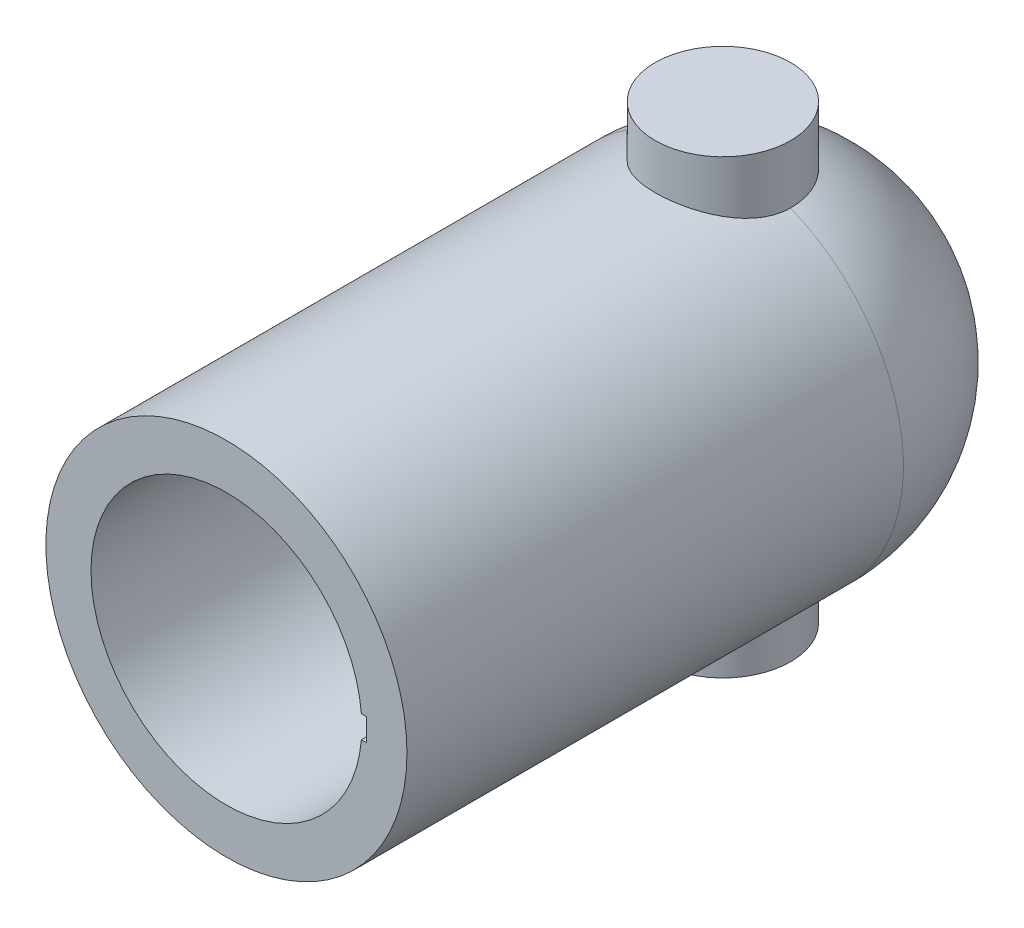
SolidWorks part; units mm, degrees
ref_plane "Front Plane" through (0, 0, 0) normal (0, 0, 1) x (1, 0, 0)
ref_plane "Top Plane" through (0, 0, 0) normal (0, 1, 0) x (1, 0, 0)
ref_plane "Right Plane" through (0, 0, 0) normal (1, 0, 0) x (0, 0, -1)
sketch "Sketch1" plane through (0, 0, 0) normal (0, 0, 1) x (1, 0, 0)
  circle A0 centre (0, 0) radius 40
  dimension "D1" = 80
extrude "Boss-Extrude2" add sketch "Sketch1" along normal blind 110
sketch "Sketch3" plane through (0, 0, 0) normal (1, 0, 0) x (0, 0, -1)
  line L0 (0, -40) -> (0, 40) construction
  line L1 (0, 40) -> (0, -40)
  arc A0 (0, 40) -> (0, -40) centre (0, 0) cw
  dimension "D2" = 40
  dimension "D1" = 0
revolve "Revolve1" add sketch "Sketch3" angle 360 about L0
sketch "Sketch4" plane through (0, 0, 0) normal (0, 1, 0) x (1, 0, 0)
  circle A0 centre (0, 0) radius 15
  dimension "D1" = 30
extrude "Boss-Extrude3" add sketch "Sketch4" along normal blind 50
sketch "Sketch5" plane through (0, 0, 0) normal (0, 1, 0) x (1, 0, 0)
  circle A0 centre (0, 0) radius 15
  dimension "D1" = 30
extrude "Boss-Extrude4" add sketch "Sketch5" against normal blind 50
sketch "Sketch6" plane through (0, 0, 110) normal (0, 0, 1) x (1, 0, 0)
  circle A0 centre (0, 0) radius 30
  dimension "D1" = 60
extrude "Cut-Extrude1" cut sketch "Sketch6" against normal blind 100
sketch "Sketch8" plane through (0, 0, 110) normal (0, 0, 1) x (1, 0, 0)
  line L1 (0, 2.5) -> (31, 2.5)
  line L2 (0, 2.5) -> (0, -2.5)
  line L3 (0, -2.5) -> (31, -2.5)
  line L4 (31, 2.5) -> (31, -2.5)
  line L5 (0, 2.5) -> (31, -2.5) construction
  line L6 (0, -2.5) -> (31, 2.5) construction
  point P0 (15.5, 0)
  point P5 (13.5063, 0)
  point P6 (23.1773, 0)
  dimension "D1" = 31
  dimension "D2" = 5
  dimension "D3" = 0
extrude "Cut-Extrude2" cut sketch "Sketch8" against normal blind 100
